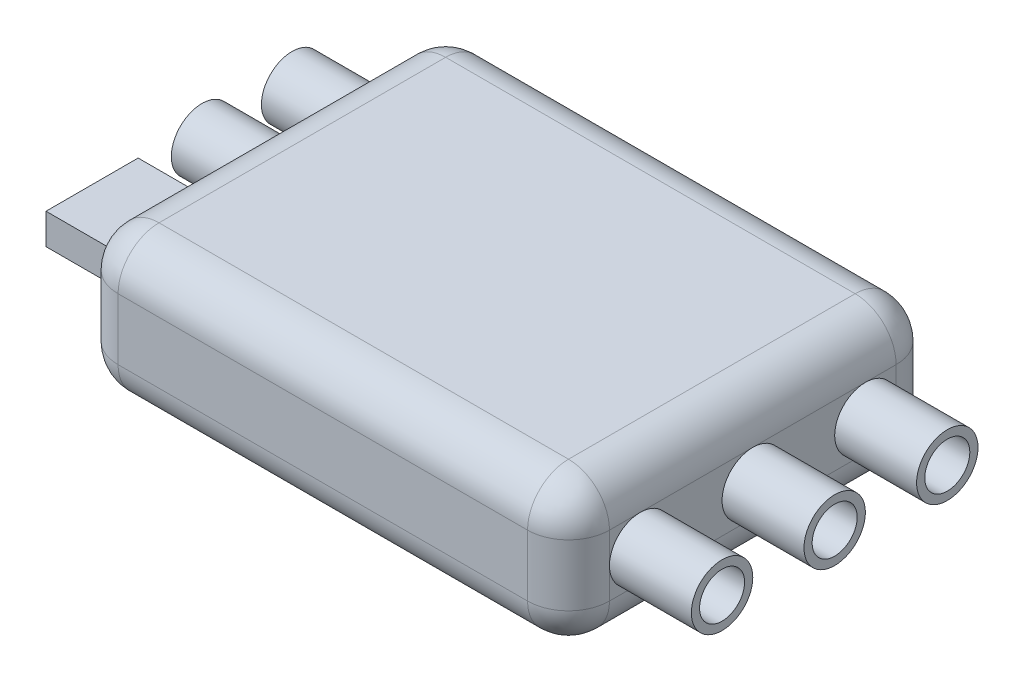
SolidWorks part; units mm, degrees
ref_plane "Front Plane" through (0, 0, 0) normal (0, 0, 1) x (1, 0, 0)
ref_plane "Top Plane" through (0, 0, 0) normal (0, 1, 0) x (1, 0, 0)
ref_plane "Right Plane" through (0, 0, 0) normal (1, 0, 0) x (0, 0, -1)
sketch "Sketch1" plane through (0, 0, 0) normal (0, 1, 0) x (1, 0, 0)
  line L1 (-10, 9) -> (10, 9)
  line L2 (-12, 7) -> (-12, -7)
  line L3 (-10, -9) -> (10, -9)
  line L4 (12, 7) -> (12, -7)
  line L5 (-12, 9) -> (12, -9) construction
  line L6 (-12, -9) -> (12, 9) construction
  arc A0 (-12, -7) -> (-10, -9) centre (-10, -7) ccw
  arc A1 (10, -9) -> (12, -7) centre (10, -7) ccw
  arc A2 (10, 9) -> (12, 7) centre (10, 7) cw
  arc A3 (-10, 9) -> (-12, 7) centre (-10, 7) ccw
  point P0 (0, 0)
  dimension "D3" = 2
  dimension "D1" = 24
  dimension "D2" = 18
extrude "Boss-Extrude1" add sketch "Sketch1" along normal blind 7
fillet "Fillet1" radius 2 16 edges at (0, 0, 9) (11.4142, 0, 8.4142) (12, 0, 0) (11.4142, 0, -8.4142) (0, 0, -9) (-11.4142, 0, -8.4142) (-12, 0, 0) (-11.4142, 0, 8.4142) (-12, 7, 0) (-11.4142, 7, -8.4142) (0, 7, -9) (11.4142, 7, -8.4142) (12, 7, 0) (11.4142, 7, 8.4142) (0, 7, 9) (-11.4142, 7, 8.4142)
sketch "Sketch2" plane through (12, 0, 0) normal (1, 0, 0) x (0, 0, -1)
  line L0 (-7, 3.5) -> (7, 3.5) construction
  line L1 (-7, 5) -> (-7, 2) construction
  line L2 (7, 5) -> (7, 2) construction
  circle A0 centre (0, 3.5) radius 1.5
  circle A1 centre (0, 3.5) radius 1.1
  circle A2 centre (-5.5, 3.5) radius 1.5
  circle A3 centre (5.5, 3.5) radius 1.5
  circle A4 centre (-5.5, 3.5) radius 1.1
  circle A5 centre (5.5, 3.5) radius 1.1
  dimension "D1" = 3
  dimension "D2" = 0.4
extrude "Boss-Extrude2" add sketch "Sketch2" along normal blind 4
sketch "Sketch3" plane through (-12, 0, 0) normal (-1, 0, 0) x (0, 0, 1)
  line L0 (-7, 3.5) -> (7, 3.5) construction
  line L1 (-7, 5) -> (-7, 2) construction
  line L2 (7, 5) -> (7, 2) construction
  line L4 (2.0204, 4.25) -> (6.5204, 4.25)
  line L5 (2.0204, 4.25) -> (2.0204, 2.75)
  line L6 (2.0204, 2.75) -> (6.5204, 2.75)
  line L7 (6.5204, 4.25) -> (6.5204, 2.75)
  circle A0 centre (-5.5, 3.5) radius 1.5
  circle A1 centre (-1.1, 3.5) radius 1.5
  circle A2 centre (-5.5, 3.5) radius 1.1
  circle A3 centre (-1.1, 3.5) radius 1.1
  dimension "D3" = 3
  dimension "D4" = 0.4
  dimension "D1" = 4.5
  dimension "D2" = 1.5
  dimension "D5" = 4.4
extrude "Boss-Extrude3" add sketch "Sketch3" along normal blind 4
